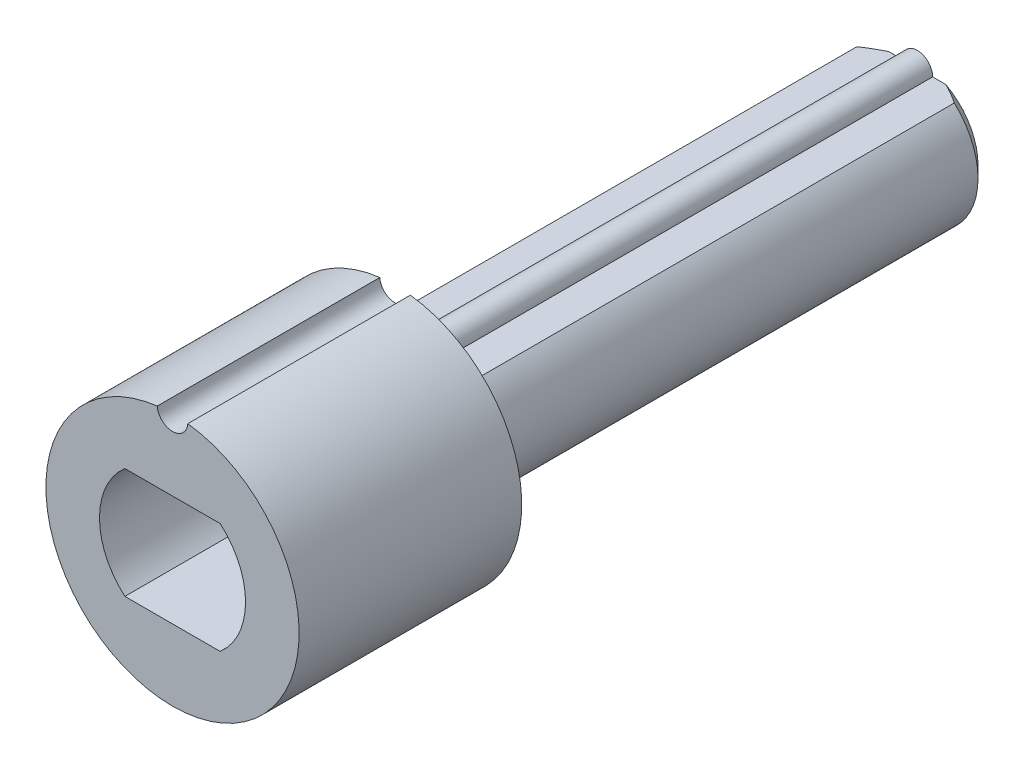
SolidWorks part; units mm, degrees
ref_plane "Спереди" through (0, 0, 0) normal (0, 0, 1) x (1, 0, 0)
ref_plane "Сверху" through (0, 0, 0) normal (0, 1, 0) x (1, 0, 0)
ref_plane "Справа" through (0, 0, 0) normal (1, 0, 0) x (0, 0, -1)
sketch "Sketch1" plane through (0, 0, 0) normal (0, 0, 1) x (1, 0, 0)
  line L0 (0.65, 2.275) -> (2.0688, 2.275)
  line L1 (-2.0688, 2.275) -> (-0.65, 2.275)
  line L3 (-2.0688, -2.275) -> (2.0688, -2.275)
  line L5 (0, -2.275) -> (0, 1.95) construction
  line L6 (-3.075, 0) -> (0, 0) construction
  arc A0 (-2.0688, 2.275) -> (-2.0688, -2.275) centre (0, 0) ccw
  arc A2 (2.0688, -2.275) -> (2.0688, 2.275) centre (0, 0) ccw
  arc A3 (0.65, 2.275) -> (-0.65, 2.275) centre (0, 2.275) ccw
  dimension "D2" = 6.15
extrude "Boss-Extrude1" add sketch "Sketch1" along normal blind 22.17
sketch "Sketch2" plane through (0, 0, 22.17) normal (0, 0, 1) x (1, 0, 0)
  arc A0 (-0.6488, 5.3357) -> (0.6488, 5.3357) centre (0, 0) ccw
  arc A2 (-0.6488, 5.3357) -> (0.6488, 5.3357) centre (0, 5.375) ccw
extrude "Boss-Extrude2" add sketch "Sketch2" along normal blind 9.45
sketch "Sketch3" plane through (0, 0, 31.62) normal (0, 0, 1) x (1, 0, 0)
  line L0 (-5.375, 0) -> (-5.375, 1.9554) construction
  line L1 (-2.0218, 2.35) -> (2.0218, 2.35)
  line L3 (-2.0218, -2.35) -> (2.0218, -2.35)
  line L5 (0, -2.35) -> (0, 2.35) construction
  line L6 (-3.1, 0) -> (2.0218, 0) construction
  arc A0 (-2.0218, 2.35) -> (-2.0218, -2.35) centre (0, 0) ccw
  arc A1 (2.0218, -2.35) -> (2.0218, 2.35) centre (0, 0) ccw
  arc A2 (-0.6488, 5.3357) -> (0.6488, 5.3357) centre (0, 0) ccw construction
extrude "Cut-Extrude1" cut sketch "Sketch3" against normal blind 6.8
chamfer "Chamfer1" distance 0.5 angle 45 2 edges at (3.075, 0, 0) (-3.075, 0, 0)
